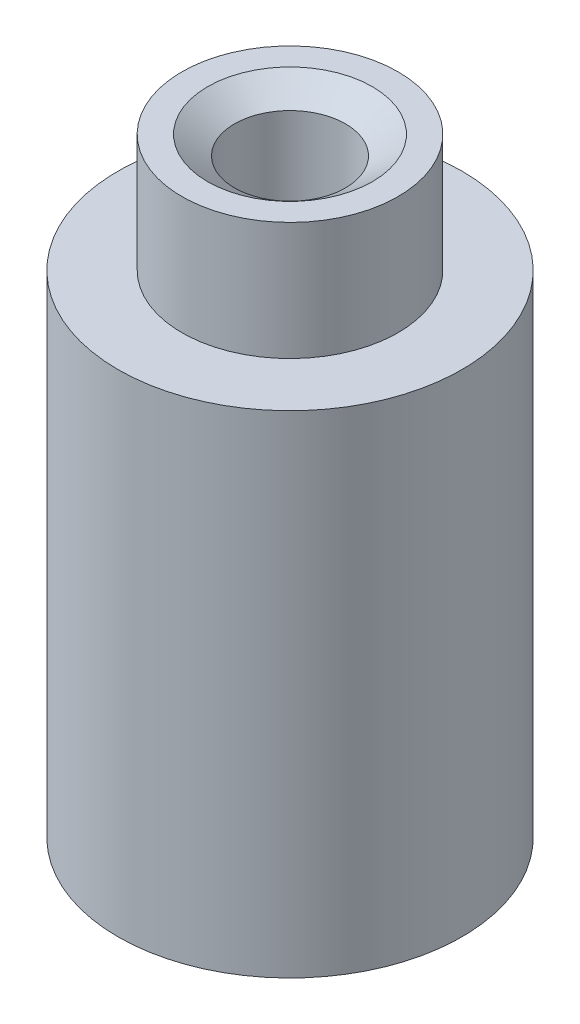
SolidWorks part; units mm, degrees
material "2024-T4"
ref_plane "Спереди" through (0, 0, 0) normal (0, 0, 1) x (1, 0, 0)
ref_plane "Сверху" through (0, 0, 0) normal (0, 1, 0) x (1, 0, 0)
ref_plane "Справа" through (0, 0, 0) normal (1, 0, 0) x (0, 0, -1)
sketch "Эскиз1" plane through (0, 0, 0) normal (1, 0, 0) x (0, 0, -1)
  line L0 (0, 0) -> (0, 12.4)
  line L1 (0, 12.4) -> (2.2, 12.4)
  line L2 (2.2, 12.4) -> (2.2, 10)
  line L3 (2.2, 10) -> (3.5, 10)
  line L4 (3.5, 10) -> (3.5, 0)
  line L5 (3.5, 0) -> (0, 0)
  dimension "D1" = 2.2
  dimension "D2" = 2.4
  dimension "D3" = 10
  dimension "D4" = 3.5
revolve "Повернуть1" add sketch "Эскиз1" angle 360 about L0
hole_wizard "Отверстие обработанное метчиком #4-401" positions "Эскиз3" profile "Эскиз2" tap size "#4-40" standard "Ansi (в дюймах)" end condition through all
sketch "Эскиз3" plane through (0, 0, 0) normal (0, -1, 0) x (1, 0, 0)
  circle A0 centre (0, 0) radius 3.5 construction
  point P0 (0, 0)
sketch "Эскиз2" plane through (0, 0, 0) normal (1, 0, 0) x (0, 0, -1)
  line L0 (0, 0) -> (0, 12.4)
  line L1 (0, 12.4) -> (1.6764, 12.4)
  line L2 (1.1303, 12.0176) -> (1.1303, 0.3824)
  line L3 (1.1303, 0.3824) -> (1.6764, 0)
  line L5 (1.6764, 0) -> (0, 0)
  line L6 (-1.1303, 0.3824) -> (-1.6764, 0) construction
  line L7 (1.6764, 12.4) -> (1.1303, 12.0176)
  line L8 (-1.6764, 12.4) -> (-1.1303, 12.0176) construction
  line L11 (0, -6.35) -> (0, 107.95) construction
  dimension "Диаметр проходного сверла" = 2.2606
  dimension "Глубина проходного сверла" = 12.4
  dimension "Диаметр передней зенковки" = 3.3528
  dimension "Угол передней зенковки" = 110
  dimension "Диаметр задней зенковки" = 3.3528
  dimension "Угол задней зенковки" = 110
cosmetic thread "Отверстие резьбы1"
